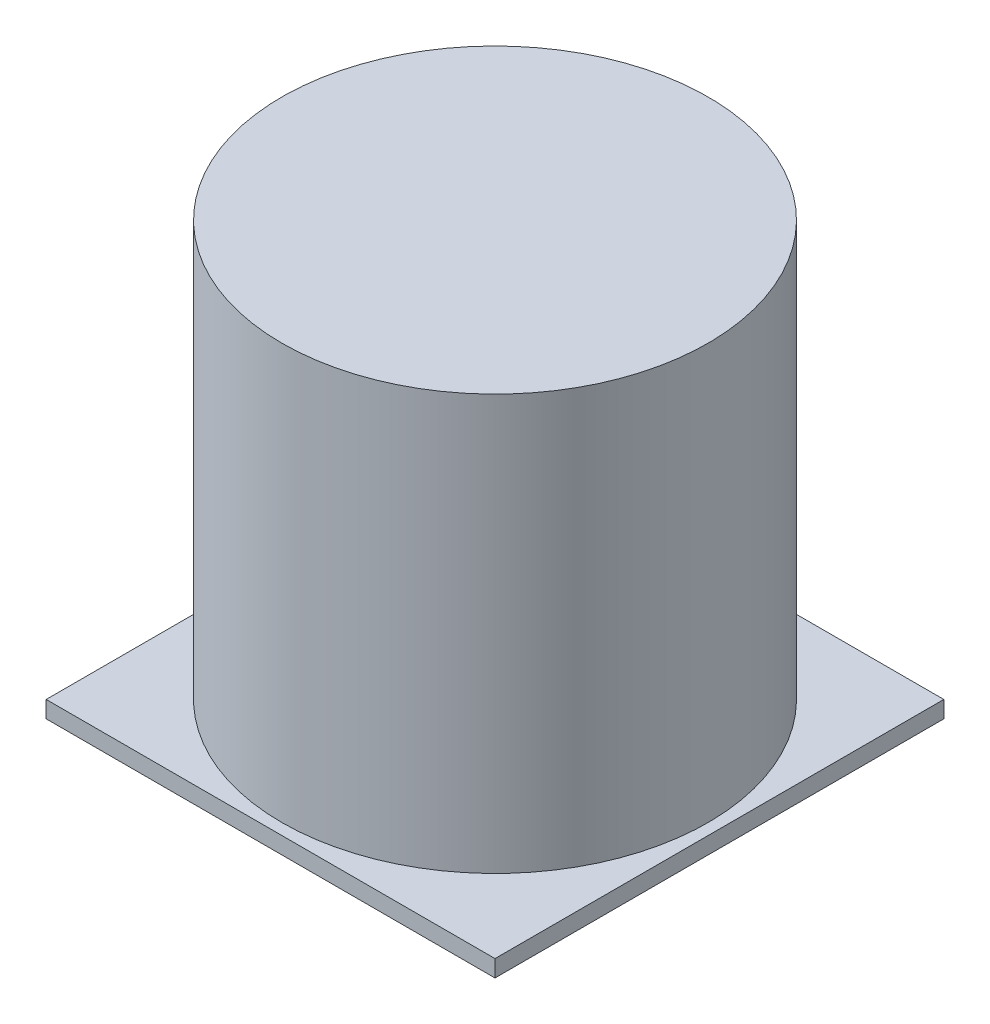
SolidWorks part; units mm, degrees
ref_plane "Front Plane" through (0, 0, 0) normal (0, 0, 1) x (1, 0, 0)
ref_plane "Top Plane" through (0, 0, 0) normal (0, 1, 0) x (1, 0, 0)
ref_plane "Right Plane" through (0, 0, 0) normal (1, 0, 0) x (0, 0, -1)
sketch "Sketch1" plane through (0, 0, 0) normal (0, 1, 0) x (1, 0, 0)
  line L0 (0, 40) -> (0, -40)
  line L1 (0, -40) -> (80, -40)
  line L2 (80, -40) -> (80, 40)
  line L3 (80, 40) -> (0, 40)
  dimension "D1" = 40
  dimension "D2" = 80
  dimension "D3" = 80
extrude "Boss-Extrude1" add sketch "Sketch1" along normal blind 3
sketch "Sketch3" plane through (0, 3, 0) normal (0, 1, 0) x (1, 0, 0)
  line L4 (80, -40) -> (80, 40) construction
  line L5 (0, -40) -> (80, -40) construction
  circle A0 centre (40, 0) radius 38
  dimension "D3" = 76
  dimension "D1" = 40
  dimension "D2" = 40
extrude "Extrude-Thin1" add sketch "Sketch3" along normal blind 74 thin thin type one direction reverse wall 3
sketch "Sketch7" plane through (0, 0, 0) normal (0, 0, 1) x (1, 0, 0)
  line L0 (40, 77) -> (2, 77)
  line L1 (75, 77) -> (5, 77) construction
  line L2 (2, 77) -> (2, 36)
  line L3 (2, 77) -> (2, 3) construction
  line L4 (40, 74) -> (2, 36)
  line L5 (40, 77) -> (40, -4.4067) construction
  line L6 (40, -4.4067) -> (40, 95.4261) construction
  line L7 (40, 77) -> (40, 74)
  dimension "D1" = 3
  dimension "D2" = 45
revolve "Revolve5" add sketch "Sketch7" angle 360 about L5
